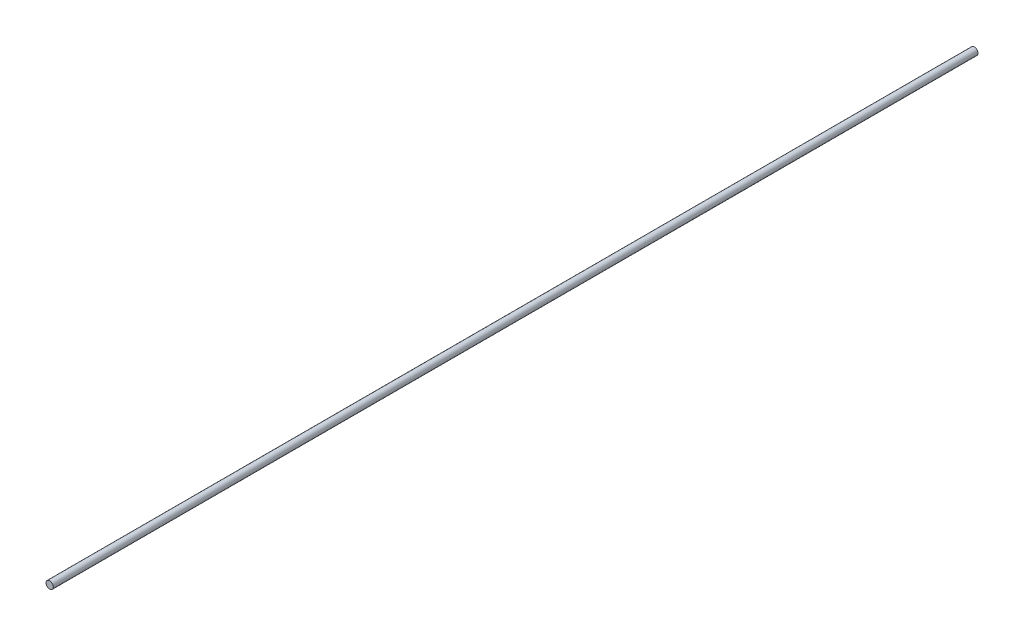
SolidWorks part; units mm, degrees
material "AISI 316 Annealed Stainless Steel Bar (SS)"
ref_plane "Front Plane" through (0, 0, 0) normal (0, 0, 1) x (1, 0, 0)
ref_plane "Top Plane" through (0, 0, 0) normal (0, 1, 0) x (1, 0, 0)
ref_plane "Right Plane" through (0, 0, 0) normal (1, 0, 0) x (0, 0, -1)
sketch "Sketch1" plane through (0, 0, 0) normal (0, 0, 1) x (1, 0, 0)
  circle A0 centre (0, 0) radius 2.5
extrude "Boss-Extrude1" add sketch "Sketch1" against normal blind 635
